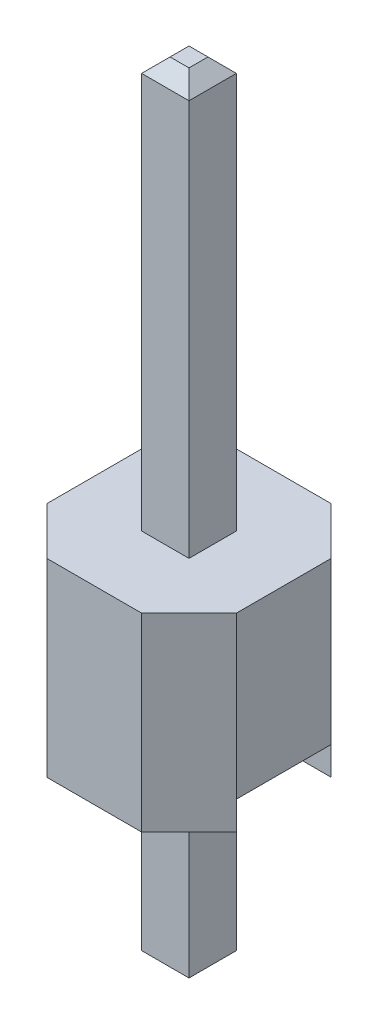
SolidWorks part; units mm, degrees
material "Plain Carbon Steel"
ref_plane "Front Plane" through (0, 0, 0) normal (0, 0, 1) x (1, 0, 0)
ref_plane "Top Plane" through (0, 0, 0) normal (0, 1, 0) x (1, 0, 0)
ref_plane "Right Plane" through (0, 0, 0) normal (1, 0, 0) x (0, 0, -1)
sketch "Sketch1" plane through (0, 0, 0) normal (0, 1, 0) x (1, 0, 0)
  line L0 (0.635, 1.27) -> (1.27, 0.635)
  line L1 (-0.635, -1.27) -> (0.635, -1.27)
  line L2 (-1.27, -0.635) -> (-1.27, 0.635)
  line L3 (-0.635, 1.27) -> (0.635, 1.27)
  line L4 (1.27, -0.635) -> (1.27, 0.635)
  line L5 (-0.9525, -0.9525) -> (0.9525, 0.9525) construction
  line L6 (-0.9525, 0.9525) -> (0.9525, -0.9525) construction
  line L7 (1.27, -0.635) -> (0.635, -1.27)
  line L8 (-0.635, -1.27) -> (-1.27, -0.635)
  line L9 (-1.27, 0.635) -> (-0.635, 1.27)
  point P0 (0, 0)
  point P17 (0, 0)
  dimension "D4" = 4
extrude "Boss-Extrude1" add sketch "Sketch1" along normal blind 2.54
sketch "Sketch2" plane through (1.27, 0, 0) normal (1, 0, 0) x (0, 0, -1)
  line L0 (-0.635, 0) -> (0.635, 0)
  line L2 (-0.635, 0) -> (-0.635, 0.381)
  line L3 (-0.635, 0.381) -> (0.635, 0.381)
  line L4 (0.635, 0) -> (0.635, 0.381)
  point P0 (0, 0)
extrude "Cut-Extrude1" cut sketch "Sketch2" against normal up to surface (2.54 mm away) up to face at (-1.27, 1.27, 0)
sketch "Sketch3" plane through (0, 2.54, 0) normal (0, 1, 0) x (1, 0, 0)
  line L1 (-0.3175, -0.3175) -> (0.3175, -0.3175)
  line L2 (-0.3175, -0.3175) -> (-0.3175, 0.3175)
  line L3 (-0.3175, 0.3175) -> (0.3175, 0.3175)
  line L4 (0.3175, -0.3175) -> (0.3175, 0.3175)
  line L5 (-0.3175, -0.3175) -> (0.3175, 0.3175) construction
  line L6 (-0.3175, 0.3175) -> (0.3175, -0.3175) construction
  point P0 (0, 0)
  dimension "D1" = 0.635
extrude "Boss-Extrude2" add sketch "Sketch3" along normal blind 5.5
chamfer "Chamfer1" distance 0.1905 angle 45 4 edges at (0, 8.04, -0.3175) (0.3175, 8.04, 0) (-0.3175, 8.04, 0) (0, 8.04, 0.3175)
sketch "Sketch4" plane through (0, 0.381, 0) normal (0, -1, 0) x (1, 0, 0)
  line L1 (-0.3175, -0.3175) -> (0.3175, -0.3175)
  line L2 (-0.3175, -0.3175) -> (-0.3175, 0.3175)
  line L3 (-0.3175, 0.3175) -> (0.3175, 0.3175)
  line L4 (0.3175, -0.3175) -> (0.3175, 0.3175)
  line L5 (-0.3175, -0.3175) -> (0.3175, 0.3175) construction
  line L6 (-0.3175, 0.3175) -> (0.3175, -0.3175) construction
  point P0 (0, 0)
  dimension "D1" = 0.635
extrude "Boss-Extrude3" add sketch "Sketch4" along normal blind 2.9
chamfer "Chamfer2" distance 0.1905 angle 45 4 edges at (-0.3175, -2.519, 0) (0, -2.519, -0.3175) (0.3175, -2.519, 0) (0, -2.519, 0.3175)
